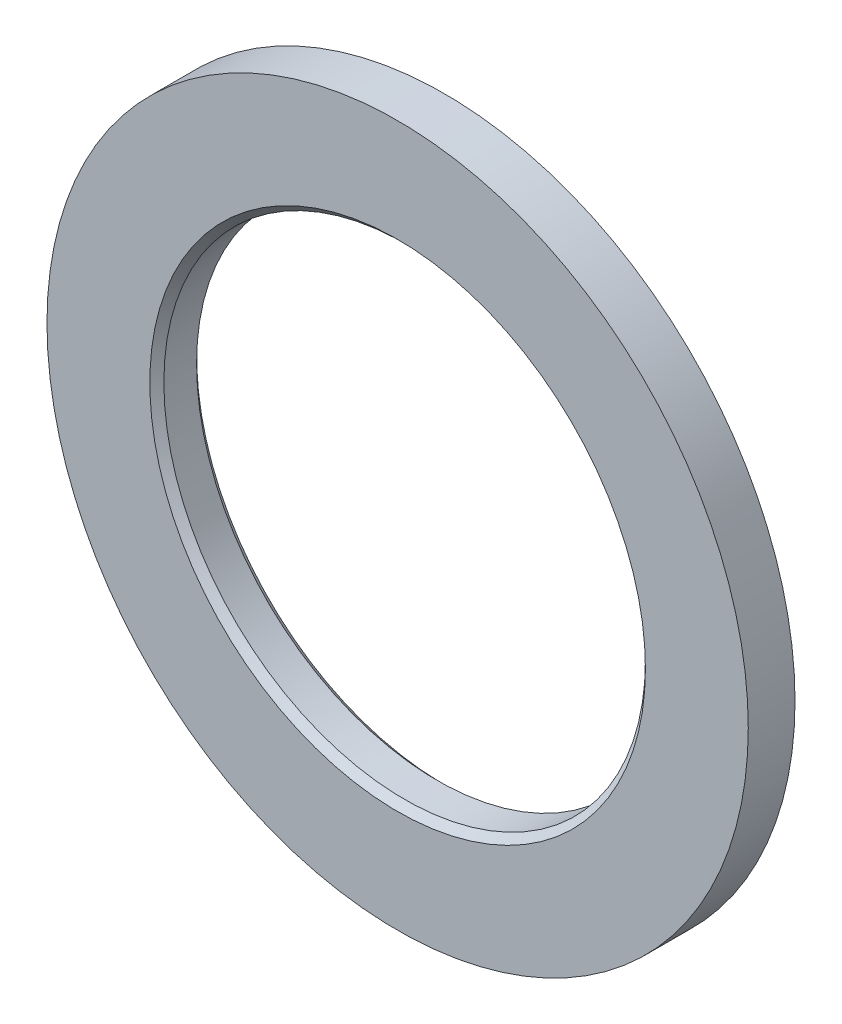
SolidWorks part; units mm, degrees
ref_plane "Front" through (0, 0, 0) normal (0, 0, 1) x (1, 0, 0)
ref_plane "Top" through (0, 0, 0) normal (0, 1, 0) x (1, 0, 0)
ref_plane "Right" through (0, 0, 0) normal (1, 0, 0) x (0, 0, -1)
sketch "Guard base" plane through (0, 0, 0) normal (0, 0, 1) x (1, 0, 0)
  circle A0 centre (0, 0) radius 37.5
  dimension "D1" = 75
extrude "Guard" add sketch "Guard base" along normal blind 5
sketch "Axle hole base" plane through (0, 0, 5) normal (0, 0, 1) x (1, 0, 0)
  circle A0 centre (0, 0) radius 25.75
  dimension "D1" = 51.5
extrude "Axle hole" cut sketch "Axle hole base" against normal through all
ref_axis "Center Z" through (0, 0, 0) along (0, 0, -1)
sketch "Mate ring room base" plane through (0, 0, 0) normal (0, 1, 0) x (1, 0, 0)
  line L0 (25.75, -5) -> (26.5, -5)
  line L1 (26.5, -5) -> (25.75, -4.25)
  line L2 (25.75, -4.25) -> (25.75, -5)
  line L5 (25.75, 0) -> (26.5, 0)
  line L6 (25.75, 0) -> (25.75, -0.75)
  line L7 (25.75, -0.75) -> (26.5, 0)
  dimension "D1" = 0.75
revolve "Mate ring room" cut sketch "Mate ring room base" angle 360 about axis through (0, 0, 0) along (0, 0, -1)
equation "\"mate_room\"= 0.25"
equation "\"removal_room\"= 0.75"
equation "\"large_inner_axle_diameter\"=20"
equation "\"D1@Axle hole base\"=\"52_62_spool_inner_diameter\"-\"spool_inner_diameter_room\"+\"mate_room\"*2"
equation "\"guard_thickness\"=5"
equation "\"spool_inner_diameter_room\"=1"
equation "\"D1@Guard\"=\"guard_thickness\""
equation "\"32_92_guard_diameter\"=50"
equation "\"D1@Guard base\"=\"52_62_guard_diameter\""
equation "\"32_92_spool_inner_diameter\"=32"
equation "\"32_92_spool_thickness\"=92"
equation "\"D1@Mate ring room base\" = \"removal_room\""
equation "\"bend_room_length_multiplier\"=3"
equation "\"small_inner_axle_diameter\"=17"
equation "\"32_92_extra_spool_thickness\"=-5"
equation "\"39_92_spool_inner_diameter\"=39"
equation "\"39_92_spool_thickness\"=92"
equation "\"39_92_guard_diameter\"=60"
equation "\"53_55_spool_inner_diameter\"=53"
equation "\"53_55_spool_thickness\"=55"
equation "\"53_55_guard_diameter\"=75"
equation "\"52_62_spool_inner_diameter\"=52"
equation "\"52_62_spool_thickness\"=62"
equation "\"52_62_guard_diameter\"=75"
